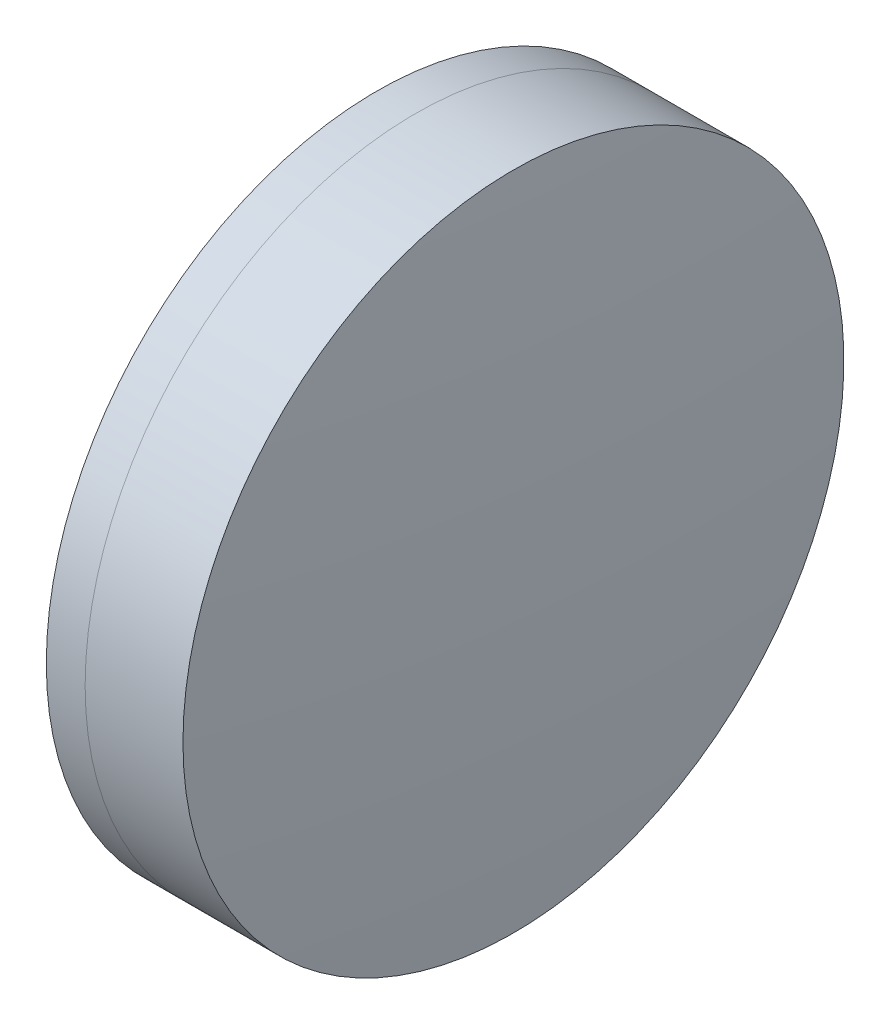
SolidWorks part; units mm, degrees
ref_plane "前视基准面" through (0, 0, 0) normal (0, 0, 1) x (1, 0, 0)
ref_plane "上视基准面" through (0, 0, 0) normal (0, 1, 0) x (1, 0, 0)
ref_plane "右视基准面" through (0, 0, 0) normal (1, 0, 0) x (0, 0, -1)
sketch "草图1" plane through (0, 0, 0) normal (0, 1, 0) x (1, 0, 0)
  line L0 (235.8075, 0) -> (276.2609, 0) construction
  line L1 (264.0421, -12.7) -> (265.5341, -12.7)
  line L2 (264.0421, 12.7) -> (265.5341, 12.7)
  arc A0 (265.5341, -12.7) -> (265.5341, 12.7) centre (211.0958, 0) ccw
  arc A1 (264.0421, 12.7) -> (264.0421, -12.7) centre (340.5958, 0) ccw
  point P4 (276.2609, 0)
  point P6 (235.8075, 0)
  point P10 (262.9958, 0)
  point P11 (266.9958, 0)
  dimension "D3" = 77.6
  dimension "D4" = 55.9
  dimension "D1" = 12.7
  dimension "D2" = 12.7
  dimension "D5" = 4
revolve "旋转1" add sketch "草图1" angle 360 about L0
sketch "草图2" plane through (0, 0, 0) normal (0, 1, 0) x (1, 0, 0)
  line L0 (-0.5519, 0) -> (279.7464, 0) construction
  line L2 (265.5341, 12.7) -> (269.2935, 12.7)
  line L3 (265.5341, -12.7) -> (269.2935, -12.7)
  arc A0 (269.2935, -12.7) -> (269.2935, 12.7) centre (108.9958, 0) ccw
  arc A1 (265.5341, -12.7) -> (265.5341, 12.7) centre (211.0958, 0) ccw construction
  arc A2 (265.5341, -12.7) -> (265.5341, 12.7) centre (211.0958, 0) ccw
  point P4 (266.9958, 0)
  point P8 (269.7958, 0)
  point P9 (279.7464, 0)
  dimension "D1" = 160.8
  dimension "D2" = 2.8
revolve "旋转3" add sketch "草图2" angle 360 about L0
